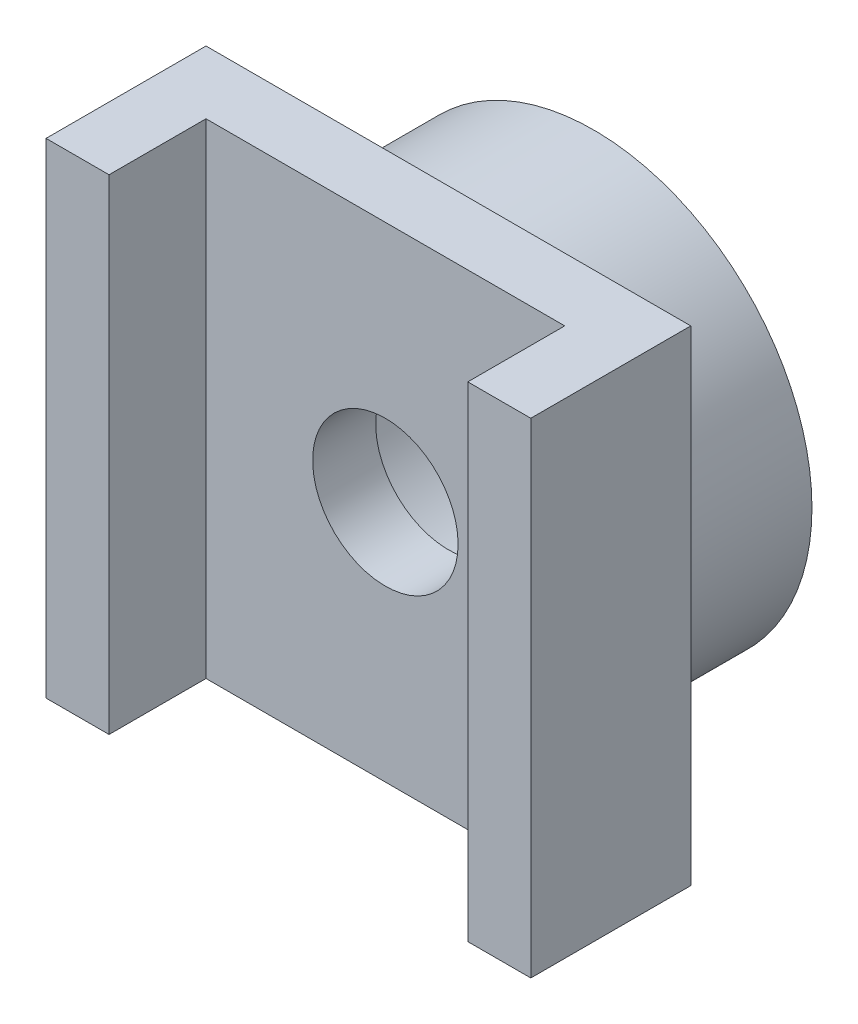
SolidWorks part; units mm, degrees
material "ABS"
ref_plane "Front Plane" through (0, 0, 0) normal (0, 0, 1) x (1, 0, 0)
ref_plane "Top Plane" through (0, 0, 0) normal (0, 1, 0) x (1, 0, 0)
ref_plane "Right Plane" through (0, 0, 0) normal (1, 0, 0) x (0, 0, -1)
sketch "Sketch1" plane through (0, 0, 0) normal (0, 0, 1) x (1, 0, 0)
  circle A0 centre (0, 0) radius 4.5
  circle A1 centre (0, 0) radius 2.8
  dimension "D1" = 9
  dimension "D2" = 5.6
extrude "Boss-Extrude1" add sketch "Sketch1" along normal blind 3
sketch "Sketch2" plane through (0, 0, 3) normal (0, 0, 1) x (1, 0, 0)
  line L5 (-5, -5) -> (5, -5)
  line L6 (-5, -5) -> (-5, 5)
  line L7 (-5, 5) -> (5, 5)
  line L8 (5, -5) -> (5, 5)
  line L9 (-5, -5) -> (5, 5) construction
  line L10 (-5, 5) -> (5, -5) construction
  circle A0 centre (0, 0) radius 1.5
  point P4 (0, 0)
  dimension "D2" = 3
  dimension "D1" = 10
extrude "Boss-Extrude2" add sketch "Sketch2" along normal blind 1.3
sketch "Sketch3" plane through (0, 0, 4.3) normal (0, 0, 1) x (1, 0, 0)
  line L0 (-5, -5) -> (5, -5) construction
  line L1 (-5, 5) -> (-3.7, 5)
  line L2 (-5, 5) -> (-5, -5)
  line L3 (-5, -5) -> (-3.7, -5)
  line L4 (-3.7, 5) -> (-3.7, -5)
  line L6 (5, 5) -> (3.7, 5)
  line L7 (5, 5) -> (5, -5)
  line L8 (5, -5) -> (3.7, -5)
  line L9 (3.7, 5) -> (3.7, -5)
  dimension "D1" = 1.3
extrude "Boss-Extrude3" add sketch "Sketch3" along normal blind 2
